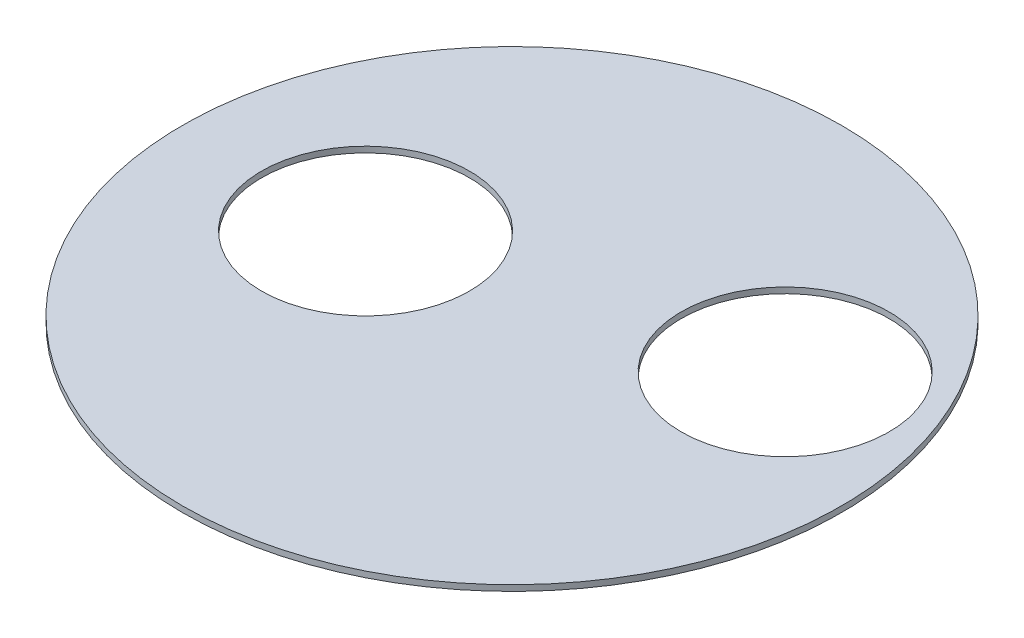
SolidWorks part; units mm, degrees
ref_plane "Ön Düzlem" through (0, 0, 0) normal (0, 0, 1) x (1, 0, 0)
ref_plane "Üst Düzlem" through (0, 0, 0) normal (0, 1, 0) x (1, 0, 0)
ref_plane "Sağ Düzlem" through (0, 0, 0) normal (1, 0, 0) x (0, 0, -1)
sketch "Çizim1" plane through (0, 0, 0) normal (0, 1, 0) x (1, 0, 0)
  circle A0 centre (0, 0) radius 112.5
  circle A1 centre (0, 0) radius 112.5 construction
  circle A4 centre (63.2456, 30) radius 35.5
  circle A6 centre (-50, 0) radius 35.5
  dimension "D1" = 71
  dimension "D2" = 30
  dimension "D3" = 70
  dimension "D5" = 50
extrude "Yükseklik-Ekstrüzyon1" add sketch "Çizim1" along normal blind 2
